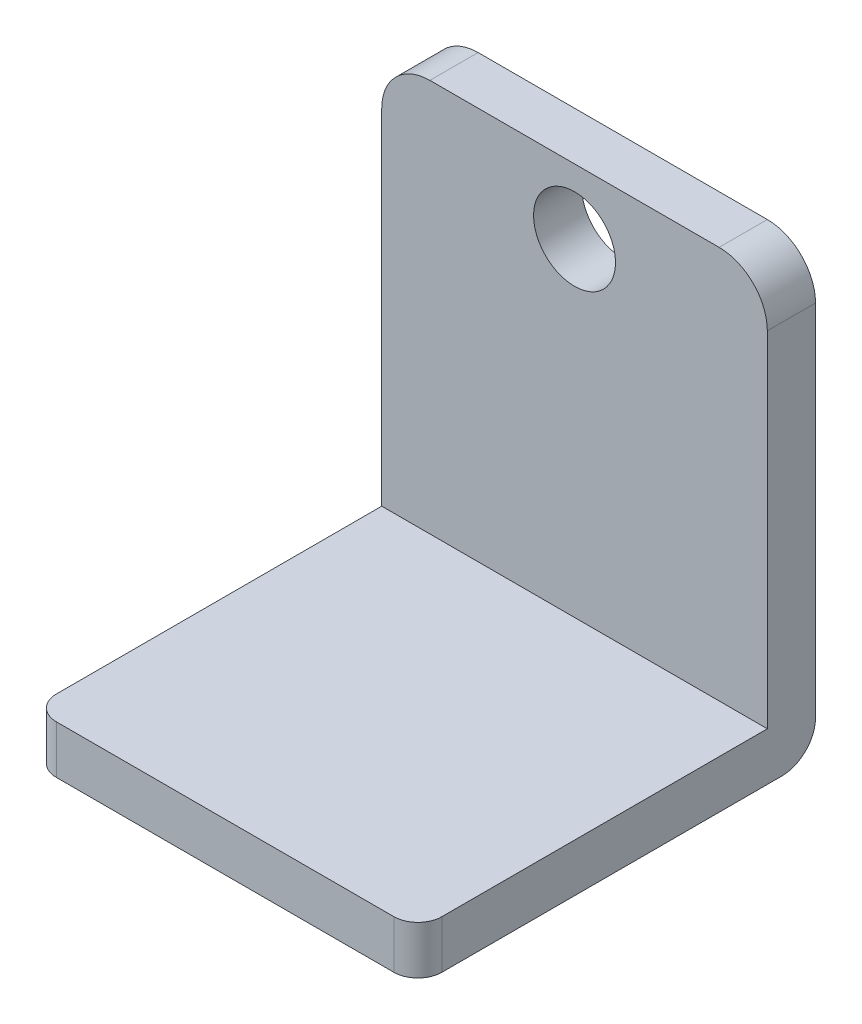
SolidWorks part; units mm, degrees
ref_plane "Front Plane" through (0, 0, 0) normal (0, 0, 1) x (1, 0, 0)
ref_plane "Top Plane" through (0, 0, 0) normal (0, 1, 0) x (1, 0, 0)
ref_plane "Right Plane" through (0, 0, 0) normal (1, 0, 0) x (0, 0, -1)
sketch "Sketch1" plane through (0, 0, 0) normal (0, 1, 0) x (1, 0, 0)
  line L1 (-99.081, 108.3174) -> (104.119, 108.3174)
  line L2 (-99.081, 108.3174) -> (-99.081, -101.2326)
  line L3 (-99.081, -101.2326) -> (104.119, -101.2326)
  line L4 (104.119, 108.3174) -> (104.119, -101.2326)
  dimension "D1" = 209.55
  dimension "8in" = 203.2
extrude "Boss-Extrude2" add sketch "Sketch1" along normal blind 25.4
sketch "Sketch2" plane through (0, 25.4, 0) normal (0, 1, 0) x (1, 0, 0)
  line L0 (104.119, -101.2326) -> (104.119, 108.3174) construction
  line L1 (-99.081, 108.3174) -> (104.119, 108.3174)
  line L2 (-99.081, 108.3174) -> (-99.081, 82.9174)
  line L3 (-99.081, 82.9174) -> (104.119, 82.9174)
  line L4 (104.119, 108.3174) -> (104.119, 82.9174)
  dimension "D1" = 25.4
extrude "Boss-Extrude3" add sketch "Sketch2" along normal blind 207.01
sketch "Sketch3" plane through (0, 0, -108.3174) normal (0, 0, -1) x (-1, 0, 0)
  line L6 (-104.119, 198.12) -> (99.081, 198.12) construction
  line L7 (-104.119, 232.41) -> (-104.119, 0) construction
  line L8 (99.081, 232.41) -> (99.081, 0) construction
  line L9 (-104.119, 232.41) -> (99.081, 232.41) construction
  circle A1 centre (-2.519, 198.12) radius 21.59
  dimension "D2" = 43.18
  dimension "D1" = 34.29
extrude "Cut-Extrude1" cut sketch "Sketch3" against normal up to next
fillet "Fillet1" radius 17.78 1 edges at (2.519, 0, -108.3174)
fillet "Fillet2" radius 25.4 2 edges at (104.119, 232.41, -95.6174) (-99.081, 232.41, -95.6174)
fillet "Fillet3" radius 12.7 2 edges at (104.119, 12.7, 101.2326) (-99.081, 12.7, 101.2326)
